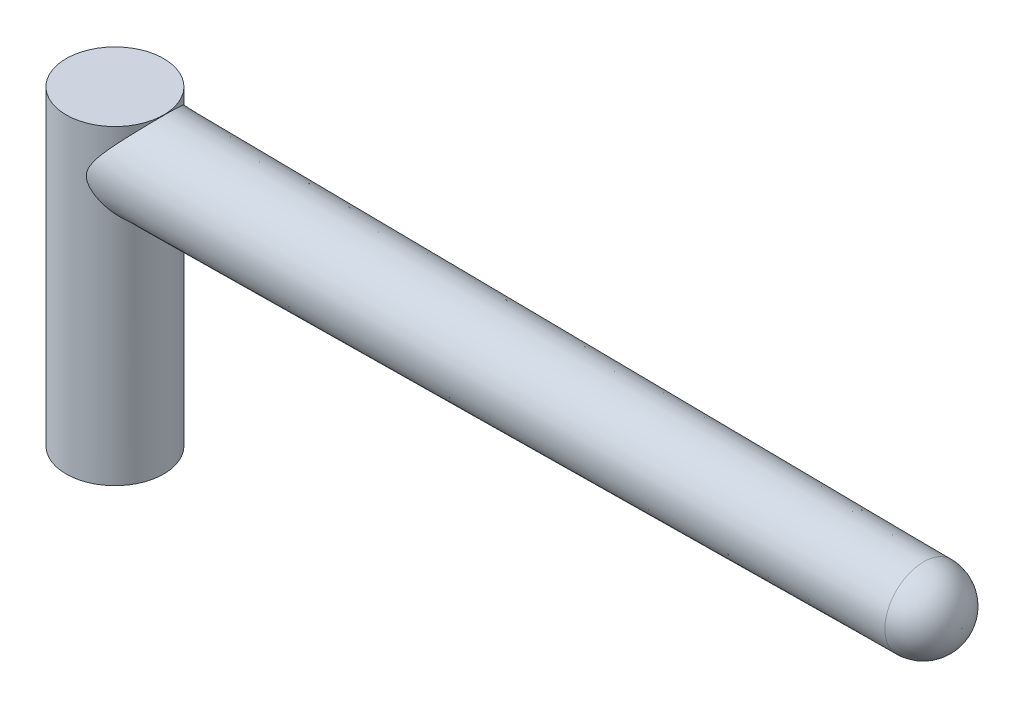
SolidWorks part; units mm, degrees
ref_plane "Front Plane" through (0, 0, 0) normal (0, 0, 1) x (1, 0, 0)
ref_plane "Top Plane" through (0, 0, 0) normal (0, 1, 0) x (1, 0, 0)
ref_plane "Right Plane" through (0, 0, 0) normal (1, 0, 0) x (0, 0, -1)
sketch "Sketch1" plane through (0, 0, 0) normal (0, 1, 0) x (1, 0, 0)
  circle A0 centre (0, 0) radius 4.95
  dimension "D1" = 9.9
extrude "Boss-Extrude1" add sketch "Sketch1" along normal blind 31.55
sketch "Sketch3" plane through (0, 0, 0) normal (1, 0, 0) x (0, 0, -1)
  line L0 (0, 5.445) -> (0, -5.445) construction
  line L1 (4.95, 31.55) -> (-4.95, 31.55) construction
  circle A0 centre (0, 26.9) radius 4.65
  dimension "D1" = 9.3
extrude "Boss-Extrude2" add sketch "Sketch3" along normal blind 85.9 draft 0.5
fillet "Fillet1" radius 3.9 1 edges at (85.9, 26.9, -3.9004)
sketch "Sketch4" plane through (0, 0, 0) normal (0, -1, 0) x (1, 0, 0)
  circle A0 centre (0, 0) radius 3.07
  dimension "D1" = 6.14
extrude "Cut-Extrude1" cut sketch "Sketch4" against normal blind 5.3
